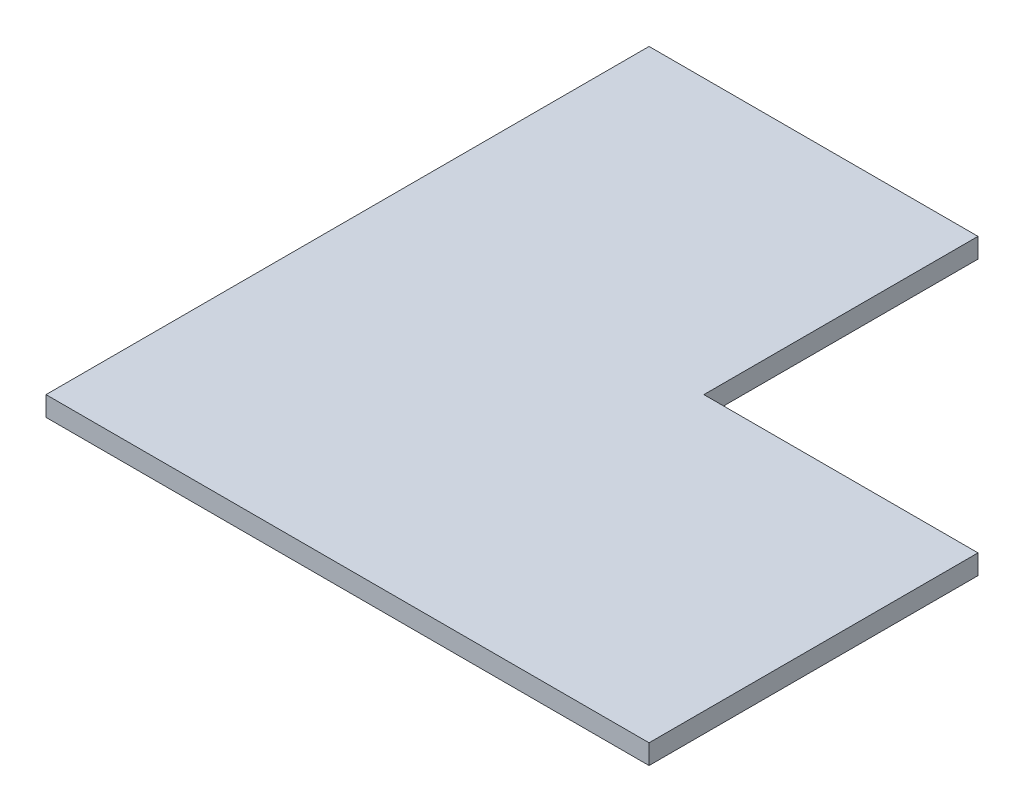
SolidWorks part; units mm, degrees
ref_plane "Спереди" through (0, 0, 0) normal (0, 0, 1) x (1, 0, 0)
ref_plane "Сверху" through (0, 0, 0) normal (0, 1, 0) x (1, 0, 0)
ref_plane "Справа" through (0, 0, 0) normal (1, 0, 0) x (0, 0, -1)
sketch "Эскиз1" plane through (0, 0, 0) normal (0, 1, 0) x (1, 0, 0)
  line L0 (0, 0) -> (0, 550)
  line L1 (0, 550) -> (300, 550)
  line L2 (300, 550) -> (300, 300)
  line L3 (300, 300) -> (550, 300)
  line L4 (550, 300) -> (550, 0)
  line L5 (550, 0) -> (0, 0)
extrude "Бобышка-Вытянуть1" add sketch "Эскиз1" along normal blind 18
